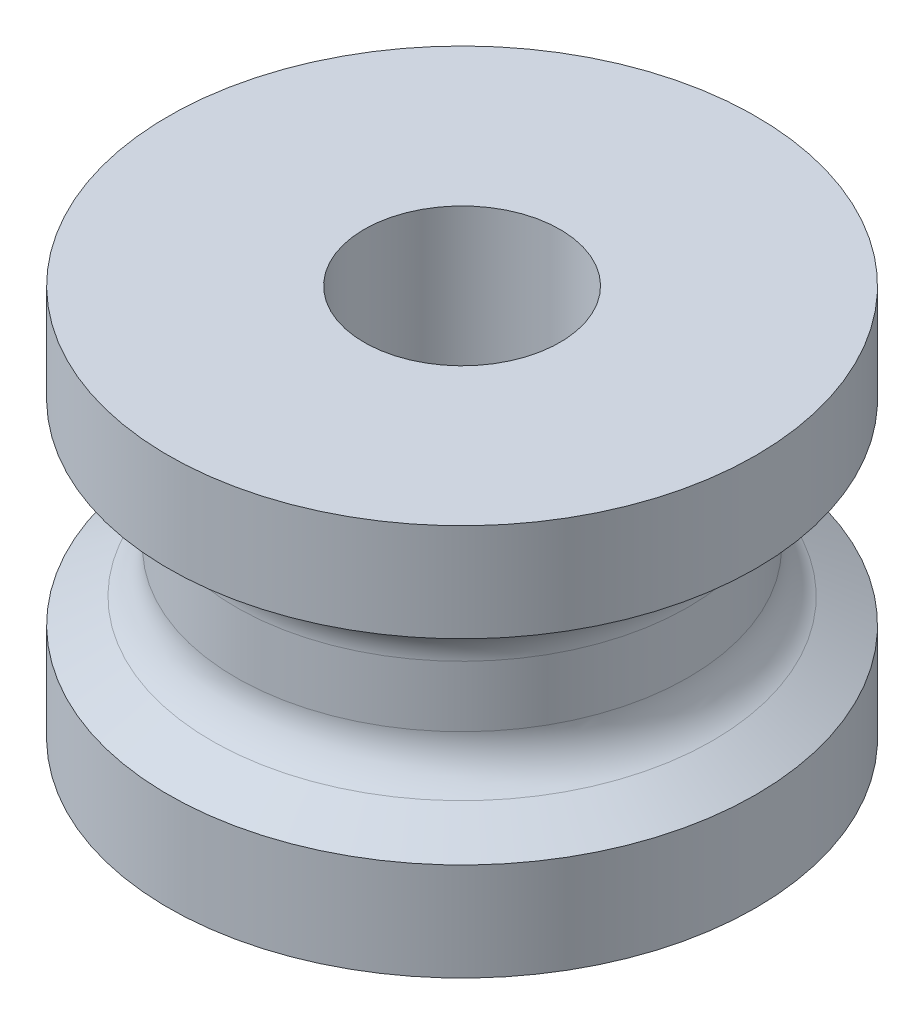
SolidWorks part; units mm, degrees
ref_plane "Front Plane" through (0, 0, 0) normal (0, 0, 1) x (1, 0, 0)
ref_plane "Top Plane" through (0, 0, 0) normal (0, 1, 0) x (1, 0, 0)
ref_plane "Right Plane" through (0, 0, 0) normal (1, 0, 0) x (0, 0, -1)
sketch "Sketch1" plane through (0, 0, 0) normal (0, 0, 1) x (1, 0, 0)
  line L0 (0, 2.5597) -> (0, 2) construction
  line L1 (0, 2) -> (3, 2)
  line L2 (3, 2) -> (3, 1)
  line L3 (0, 2) -> (0, 0) construction
  line L4 (3, 1) -> (2.5572, 0.7443)
  line L5 (2.3072, 0.3113) -> (2.3072, -0.3113)
  line L6 (0, -2) -> (0, 2)
  line L7 (0, 0) -> (2.3072, 0) construction
  line L8 (3, -1) -> (2.5572, -0.7443)
  line L9 (3, -2) -> (3, -1)
  line L10 (0, -2) -> (3, -2)
  arc A0 (2.3072, 0.3113) -> (2.5572, 0.7443) centre (2.8072, 0.3113) cw
  arc A1 (2.5572, -0.7443) -> (2.3072, -0.3113) centre (2.8072, -0.3113) cw
  point P14 (2.3072, 0.6)
  point P17 (2.3072, -0.6)
  dimension "D4" = 0.5
  dimension "D1" = 3
  dimension "D2" = 1
  dimension "D3" = 2
  dimension "D5" = 0.4
  dimension "D6" = 240
revolve "Revolve2" add sketch "Sketch1" angle 360 about L6
sketch "Sketch2" plane through (0, 2, 0) normal (0, 1, 0) x (1, 0, 0)
  circle A0 centre (0, 0) radius 1
  dimension "D1" = 2
extrude "Cut-Extrude1" cut sketch "Sketch2" against normal through all
